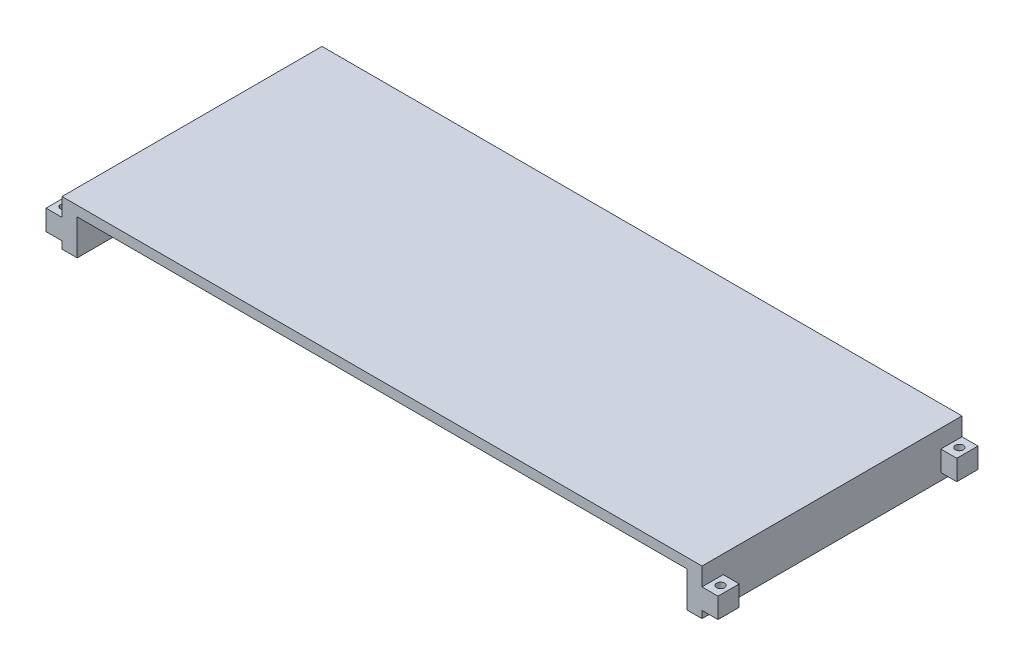
SolidWorks part; units mm, degrees
ref_plane "Front Plane" through (0, 0, 0) normal (0, 0, 1) x (1, 0, 0)
ref_plane "Top Plane" through (0, 0, 0) normal (0, 1, 0) x (1, 0, 0)
ref_plane "Right Plane" through (0, 0, 0) normal (1, 0, 0) x (0, 0, -1)
sketch "Sketch1" plane through (0, 0, 0) normal (0, 1, 0) x (1, 0, 0)
  line L0 (800, 0) -> (800, -650) construction
  line L1 (0, 0) -> (1600, 0)
  line L2 (0, 0) -> (0, -650)
  line L3 (0, -650) -> (1600, -650)
  line L4 (1600, 0) -> (1600, -650)
  dimension "D1" = 1600
  dimension "D2" = 650
  dimension "D3" = 800
extrude "Boss-Extrude1" add sketch "Sketch1" along normal blind 25
sketch "Sketch2" plane through (0, 0, 0) normal (0, -1, 0) x (1, 0, 0)
  line L0 (0, 325) -> (1600, 325) construction
  line L1 (38, 306) -> (38, 0)
  line L2 (1562, 306) -> (1562, 0)
  line L3 (0, 650) -> (1600, 650) construction
  line L4 (0, 0) -> (0, 650) construction
  line L5 (38, 344) -> (1562, 344)
  line L6 (0, 344) -> (0, 306)
  line L7 (38, 306) -> (1562, 306)
  line L8 (1600, 344) -> (1600, 306)
  line L9 (1600, 650) -> (1600, 0) construction
  line L10 (1600, 0) -> (0, 0) construction
  line L11 (0, 650) -> (38, 650)
  line L12 (0, 650) -> (0, 0)
  line L13 (0, 0) -> (38, 0)
  line L14 (38, 650) -> (38, 344)
  line L15 (1600, 650) -> (1562, 650)
  line L16 (1600, 650) -> (1600, 0)
  line L17 (1600, 0) -> (1562, 0)
  line L18 (1562, 650) -> (1562, 344)
  line M16 (0, 650) -> (0, 0)
  line M17 (0, 0) -> (1600, 0)
  line M18 (1600, 0) -> (1600, 650)
  line M19 (1600, 650) -> (0, 650)
  dimension "D1" = 325
  dimension "D2" = 38
  dimension "D3" = 19
  dimension "D4" = 38
  dimension "D5" = 38
  dimension "D6" = 38
  dimension "D7" = 38
  dimension "D8" = 38
extrude "Boss-Extrude2" add sketch "Sketch2" along normal blind 89 contours L0 L16 L18 L5 L14 M16 M18 M19 | L0 L12 L1 L7 L2 M16 M17 M18
sketch "Sketch3" plane through (0, 0, 0) normal (-1, 0, 0) x (0, 0, 1)
  line L0 (0, 25) -> (0, -89) construction
  line L1 (0, -71) -> (53, -71)
  line L2 (0, -71) -> (0, -20.2)
  line L3 (0, -20.2) -> (53, -20.2)
  line L4 (53, -71) -> (53, -20.2)
  line L5 (650, 25) -> (650, -89) construction
  line L6 (650, -71) -> (597, -71)
  line L7 (650, -71) -> (650, -20.2)
  line L8 (650, -20.2) -> (597, -20.2)
  line L9 (597, -71) -> (597, -20.2)
  line L10 (650, -89) -> (0, -89) construction
  dimension "D1" = 53
  dimension "D2" = 50.8
  dimension "D3" = 50.8
  dimension "D4" = 53
  dimension "D5" = 18
  dimension "D6" = 18
extrude "Boss-Extrude3" add sketch "Sketch3" along normal blind 40
sketch "Sketch4" plane through (0, -71, 0) normal (0, -1, 0) x (1, 0, 0)
  line L0 (-40, 53) -> (0, 53) construction
  line L1 (-40, 650) -> (0, 650) construction
  line L2 (-40, 0) -> (-40, 53) construction
  line L3 (-40, 597) -> (-40, 650) construction
  circle A0 centre (-20, 26.5) radius 10
  circle A1 centre (-20, 623.5) radius 10
  dimension "D1" = 20
  dimension "D2" = 20
  dimension "D3" = 26.5
  dimension "D4" = 26.5
  dimension "D5" = 20
  dimension "D6" = 20
extrude "Cut-Extrude1" cut sketch "Sketch4" against normal blind 129
sketch "Sketch5" plane through (0, 25, 0) normal (0, 1, 0) x (1, 0, 0)
  line L0 (800, 0) -> (800, -650)
  line L1 (1600, 0) -> (0, 0) construction
  line L2 (0, -650) -> (1600, -650) construction
sketch "Sketch6" plane through (0, 0, 0) normal (0, -1, 0) x (1, 0, 0)
  line L0 (800, 650) -> (800, 0)
ref_plane "Plane1" through (800, 0, 0) normal (1, 0, 0) x (0, 0, -1)
mirror "Mirror1" about plane through (800, 0, 0) normal (1, 0, 0) of "Cut-Extrude1", "Boss-Extrude3"
